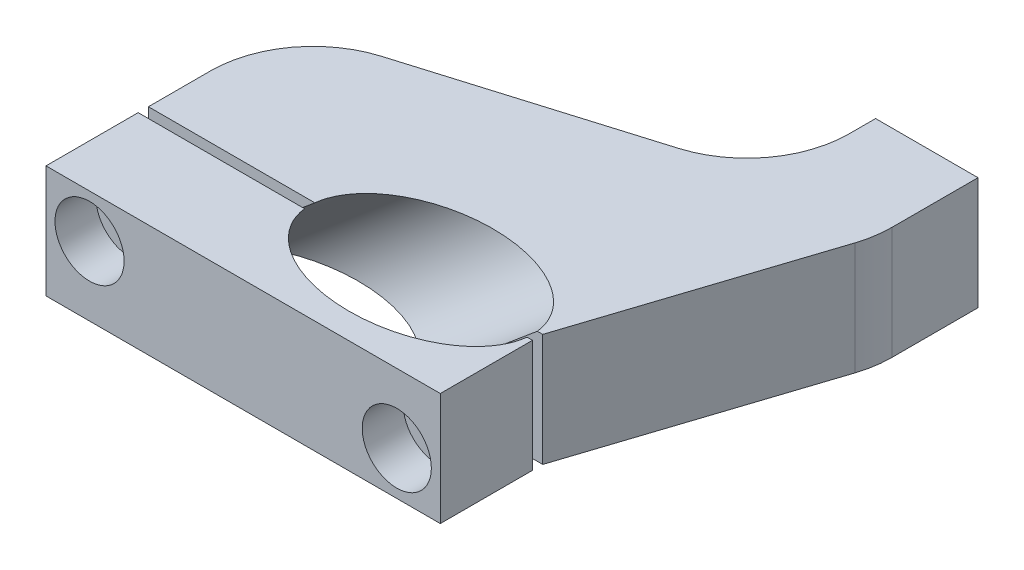
SolidWorks part; units mm, degrees
ref_plane "Plan de face" through (0, 0, 0) normal (0, 0, 1) x (1, 0, 0)
ref_plane "Plan de dessus" through (0, 0, 0) normal (0, 1, 0) x (1, 0, 0)
ref_plane "Plan de droite" through (0, 0, 0) normal (1, 0, 0) x (0, 0, -1)
sketch "Esquisse1" plane through (0, 0, 0) normal (0, 1, 0) x (1, 0, 0)
  line L0 (-5.2249, 1) -> (49994.7751, 1) construction
  line L3 (-28, 1) -> (49, 1)
  line L4 (49, -6.2865) -> (49, -50006.2865) construction
  line L5 (45, 70) -> (65, 70)
  line L6 (65, 70) -> (65, 50)
  line L7 (-28, -1) -> (49, -1)
  line L8 (49, -1) -> (49, -19)
  line L9 (49, -19) -> (-28, -19)
  line L10 (-28, 28) -> (45, 50)
  line L11 (-28, 28) -> (-28, 1)
  line L12 (-28, -1) -> (-28, -19)
  line L13 (65, 50) -> (49, 1)
  line L14 (45, 70) -> (45, 50)
  circle A0 centre (0, 0) radius 14 construction
  point P7 (-13.9642, 1)
  point P10 (45, 55)
  point P13 (0, 0)
  point P20 (0, 0)
  point P21 (0, 0)
  point P23 (-23.6729, 1)
  dimension "D1" = 28
  dimension "D3" = 20
  dimension "D5" = 27
  dimension "D6" = 77
  dimension "D9" = 18
  dimension "D2" = 1
  dimension "D4" = 20
  dimension "D7" = 70
  dimension "D8" = 65
  dimension "D11" = 1
  dimension "D12" = 28
extrude "Boss.-Extru.1" add sketch "Esquisse1" along normal blind 22
sketch "Esquisse3" plane through (0, 0, 0) normal (0, 0, 1) x (1, 0, 0)
  line L0 (-42.1324, -35.3533) -> (42.1324, 35.3533)
  line L1 (42.1324, 35.3533) -> (33.1334, 46.0779)
  line L2 (33.1334, 46.0779) -> (-51.1315, -24.6287)
  line L3 (-51.1315, -24.6287) -> (-42.1324, -35.3533)
  line L5 (-28, 0) -> (49, 0) construction
  dimension "D1" = 14
  dimension "D2" = 110
  dimension "D3" = 140
revolve "Enlèvement de matière-Révolution1" cut sketch "Esquisse3" angle 360 about L0
sketch "Esquisse4" plane through (0, 0, -70) normal (0, 0, -1) x (-1, 0, 0)
  line L1 (-45, 22) -> (28, 22) construction
  line L2 (-65, 22) -> (-65, 0) construction
  circle A0 centre (-55, 11) radius 4
  point P6 (0, 0)
  dimension "D1" = 8
  dimension "D2" = 11
  dimension "D3" = 10
extrude "Enlèv. mat.-Extru.1" cut sketch "Esquisse4" against normal blind 22
sketch "Esquisse7" plane through (0, 0, -70) normal (0, 0, -1) x (-1, 0, 0)
  line L1 (-55, 4.6491) -> (-49.5, 7.8246)
  line L2 (-49.5, 7.8246) -> (-49.5, 14.1754)
  line L3 (-49.5, 14.1754) -> (-55, 17.3509)
  line L4 (-55, 17.3509) -> (-60.5, 14.1754)
  line L5 (-60.5, 14.1754) -> (-60.5, 7.8246)
  line L6 (-60.5, 7.8246) -> (-55, 4.6491)
  circle A0 centre (-55, 11) radius 5.5 construction
  dimension "D1" = 11
fillet "Congé1" radius 20 1 edges at (45, 11, -50)
fillet "Congé2" radius 20 1 edges at (65, 11, -50)
sketch "Esquisse8" plane through (0, 0, 19) normal (0, 0, 1) x (1, 0, 0)
  line L0 (-28, 0) -> (49, 0) construction
  line L1 (49, 22) -> (49, 0) construction
  line L2 (-28, 22) -> (49, 22) construction
  line L3 (-28, 22) -> (-28, 0) construction
  circle A0 centre (40.5, 8.5) radius 6.75
  circle A1 centre (-19.5, 13.5) radius 6.75
  dimension "D1" = 13.5
  dimension "D4" = 8.5
  dimension "D2" = 8.5
  dimension "D3" = 8.5
  dimension "D5" = 8.5
extrude "Enlèv. mat.-Extru.2" cut sketch "Esquisse8" against normal blind 8 contours A1 | A0
sketch "Esquisse9" plane through (0, 0, 11) normal (0, 0, 1) x (1, 0, 0)
  circle A0 centre (-19.5, 13.5) radius 4
  circle A1 centre (40.5, 8.5) radius 4
  dimension "D1" = 8
  dimension "D2" = 8
extrude "Enlèv. mat.-Extru.3" cut sketch "Esquisse9" against normal blind 30
fillet "Congé3" radius 20 1 edges at (-28, 11, -28)
